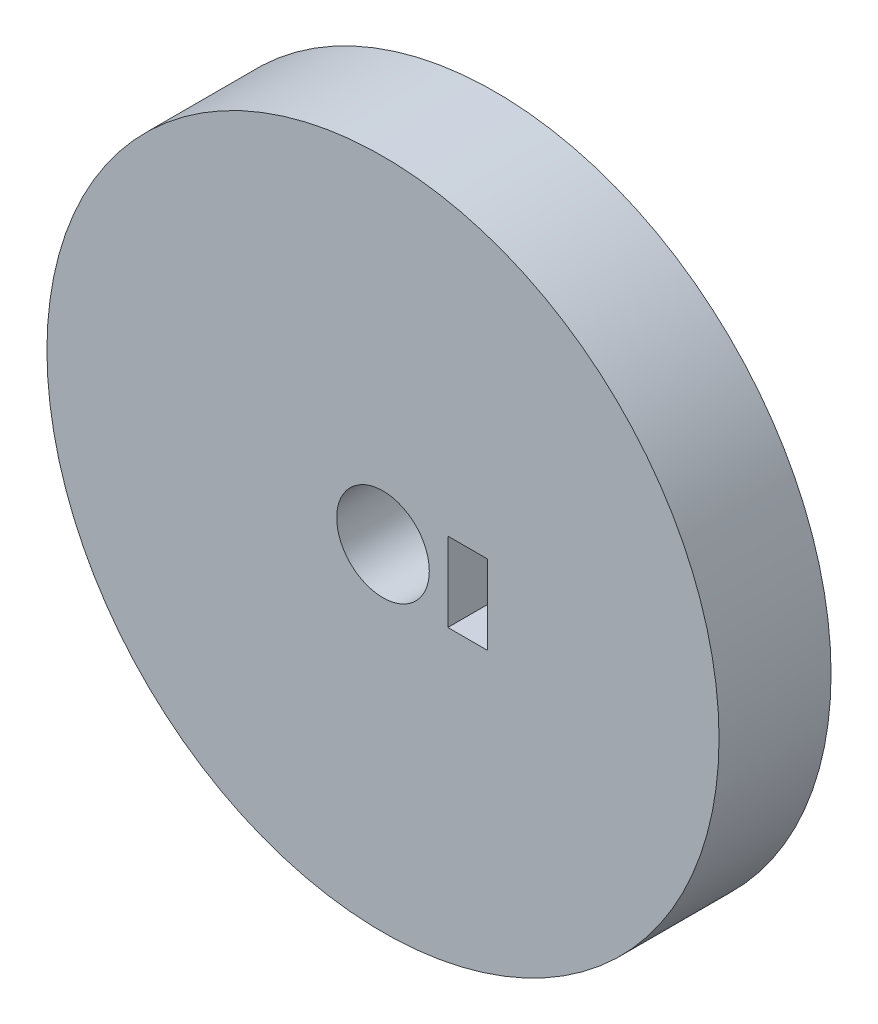
SolidWorks part; units mm, degrees
ref_plane "Front Plane" through (0, 0, 0) normal (0, 0, 1) x (1, 0, 0)
ref_plane "Top Plane" through (0, 0, 0) normal (0, 1, 0) x (1, 0, 0)
ref_plane "Right Plane" through (0, 0, 0) normal (1, 0, 0) x (0, 0, -1)
sketch "Sketch1" plane through (0, 0, 0) normal (0, 0, 1) x (1, 0, 0)
  line L0 (-71.3345, -7.0722) -> (-71.3345, -17.6722)
  line L1 (-71.3345, -17.6722) -> (-76.6345, -17.6722)
  line L2 (-76.6345, -17.6722) -> (-71.3345, -17.6722)
  line L3 (-76.6345, -7.0722) -> (-76.6345, -17.6722)
  line L4 (-71.3345, -7.0722) -> (-76.6345, -7.0722)
  line L5 (-71.3345, -17.6722) -> (-71.3345, -7.0722)
  circle A0 centre (-85.3166, -12.3722) radius 45
  circle A1 centre (-85.3166, -12.3722) radius 6.2
  dimension "D1" = 12.4
  dimension "D2" = 90
  dimension "D3" = 71.3345
  dimension "D4" = 76.6345
  dimension "D5" = 85.3166
  dimension "D6" = 7.0722
  dimension "D7" = 12.3722
  dimension "D8" = 17.6722
extrude "Boss-Extrude1" add sketch "Sketch1" along normal blind 15 contours A0 A1 L4 L0 L1 L3
